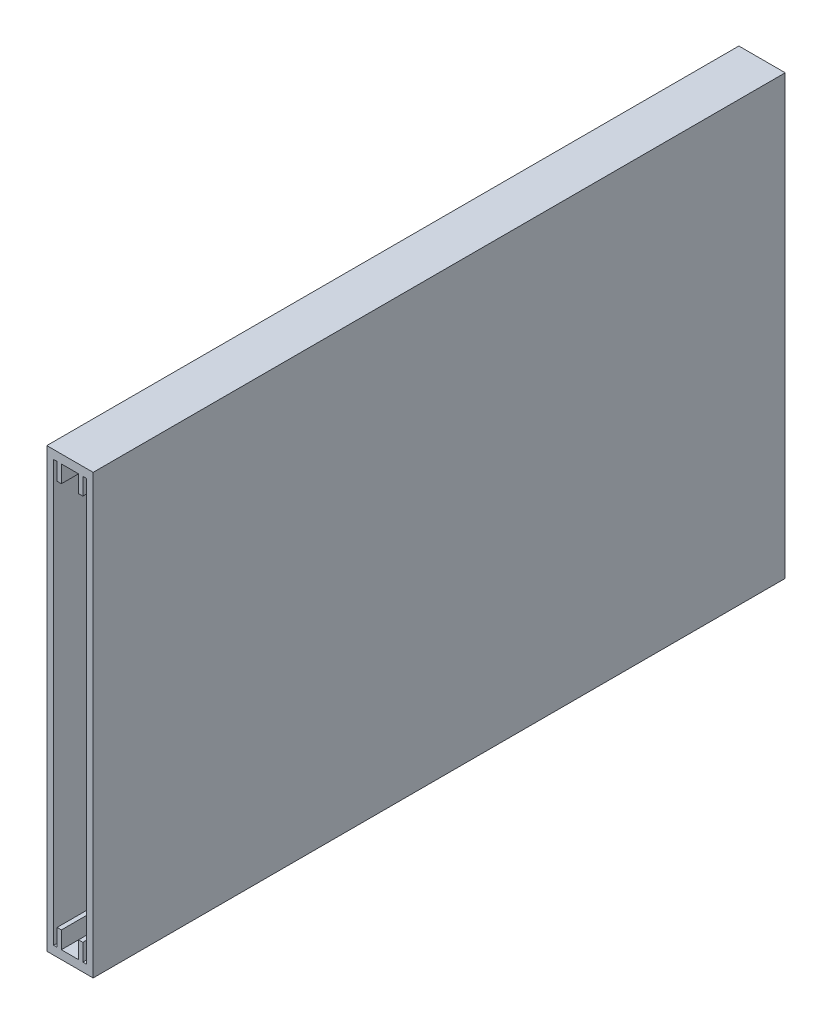
SolidWorks part; units mm, degrees
ref_plane "Ön Düzlem" through (0, 0, 0) normal (1, 0, 0) x (0, 1, 0)
ref_plane "Üst Düzlem" through (0, 0, 0) normal (0, 0, 1) x (0, 1, 0)
ref_plane "Sağ Düzlem" through (0, 0, 0) normal (0, 1, 0) x (-1, 0, 0)
sketch "Sketch1" plane through (0, 0, 0) normal (0, 0, 1) x (0, 1, 0)
  line L1 (0, 0) -> (102, 0)
  line L2 (0, 0) -> (0, 10.8)
  line L3 (0, 10.8) -> (102, 10.8)
  line L4 (102, 0) -> (102, 10.8)
  dimension "D1" = 102
  dimension "D2" = 10.8
extrude "Boss-Extrude1" add sketch "Sketch1" along normal blind 1.2
sketch "Sketch2" plane through (0, 0, 1.2) normal (0, 0, 1) x (1, 0, 0)
  line L0 (-9.2, 100) -> (-8.4, 100)
  line L1 (-10.8, 102) -> (0, 102)
  line L2 (-10.8, 102) -> (-10.8, 0)
  line L3 (-10.8, 0) -> (0, 0)
  line L4 (0, 102) -> (0, 0)
  line L5 (-1.6, 100) -> (-1.6, 2)
  line L6 (-9.2, 2) -> (-8.4, 2)
  line L7 (-9.2, 100) -> (-9.2, 2)
  line L8 (-8.4, 100) -> (-8.4, 96) construction
  line L9 (-7.4, 2) -> (-3.4, 2)
  line L11 (-2.4, 100) -> (-1.6, 100)
  line L13 (-2.4, 2) -> (-1.6, 2)
  line L14 (-7.4, 100) -> (-3.4, 100)
  line L15 (-3.4, 96) -> (-2.4, 96)
  line L16 (-3.4, 6) -> (-2.4, 6)
  line L17 (-8.4, 96) -> (-8.4, 100)
  line L18 (-2.4, 2) -> (-2.4, 6)
  line L19 (-7.4, 96) -> (-7.4, 100)
  line L20 (-3.4, 96) -> (-3.4, 100)
  line L21 (-2.4, 96) -> (-2.4, 100)
  line L22 (-8.4, 6) -> (-7.4, 6)
  line L23 (-8.4, 96) -> (-7.4, 96)
  line L24 (-3.4, 2) -> (-3.4, 6)
  line L25 (-7.4, 2) -> (-7.4, 6)
  line L26 (-8.4, 2) -> (-8.4, 6)
  dimension "D2" = 4
  dimension "D3" = 4
  dimension "D4" = 4
  dimension "D5" = 0.8
  dimension "D1" = 0.8
  dimension "D6" = 1
  dimension "D7" = 1
  dimension "D8" = 4
  dimension "D9" = 1.6
  dimension "D10" = 1
  dimension "D11" = 1
  dimension "D12" = 0.8
  dimension "D13" = 0.8
  dimension "D15" = 1.6
  dimension "D14" = 10.8
extrude "Boss-Extrude2" add sketch "Sketch2" along normal blind 160
